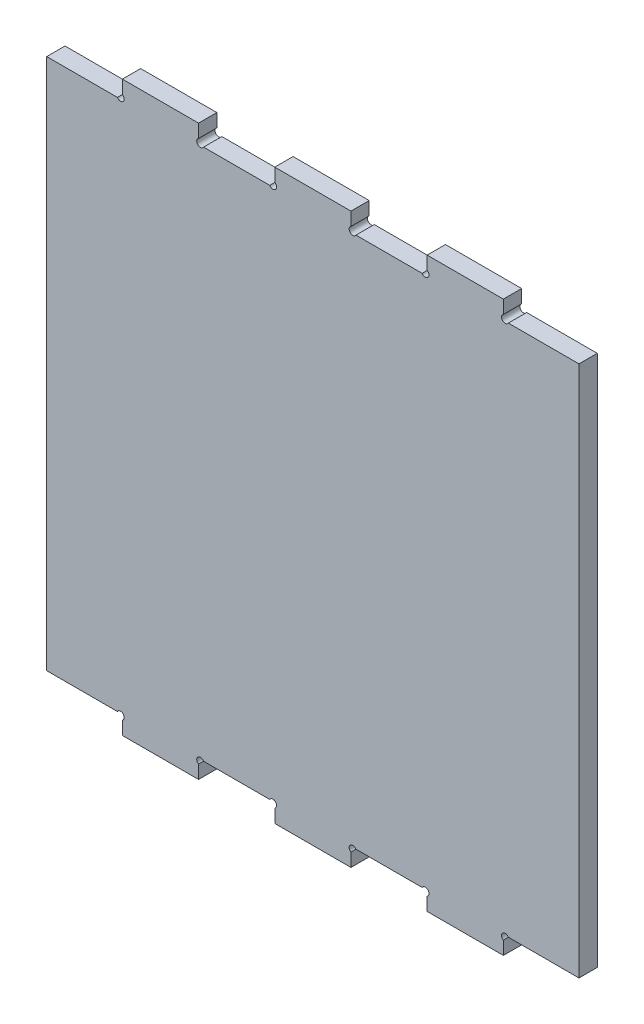
SolidWorks part; units mm, degrees
ref_plane "Front Plane" through (0, 0, 0) normal (0, 0, 1) x (1, 0, 0)
ref_plane "Top Plane" through (0, 0, 0) normal (0, 1, 0) x (1, 0, 0)
ref_plane "Right Plane" through (0, 0, 0) normal (1, 0, 0) x (0, 0, -1)
sketch "Sketch1" plane through (0, 0, 0) normal (0, 0, 1) x (1, 0, 0)
  line L0 (-147.5564, 174.6264) -> (-101.1926, 174.6264)
  line L1 (-97.9177, 186.6264) -> (-47.9177, 186.6264)
  line L2 (-147.5564, 174.6264) -> (-147.5564, -174.3736)
  line L3 (127.0823, -168.3736) -> (127.0823, -214.3646) construction
  line L4 (201.721, 174.6264) -> (201.721, -174.3736)
  line L5 (-97.9177, 168.6264) -> (-47.9177, 168.6264) construction
  line L6 (-47.9177, 186.6264) -> (-47.9177, 177.911)
  line L7 (-44.6428, 174.6264) -> (-1.1926, 174.6264)
  line L8 (2.0823, 177.911) -> (2.0823, 186.6264)
  line L9 (2.0823, 186.6264) -> (52.0823, 186.6264)
  line L10 (52.0823, 186.6264) -> (52.0823, 177.911)
  line L11 (55.3572, 174.6264) -> (98.8074, 174.6264)
  line L12 (102.0823, 177.911) -> (102.0823, 186.6264)
  line L13 (102.0823, 186.6264) -> (152.0823, 186.6264)
  line L14 (152.0823, 186.6264) -> (152.0823, 177.911)
  line L15 (155.3572, 174.6264) -> (201.721, 174.6264)
  line L16 (-72.9177, 168.6264) -> (-72.9177, 194.1917) construction
  line L17 (-47.9177, 168.6264) -> (2.0823, 168.6264) construction
  line L18 (-22.9177, 168.6264) -> (-22.9177, 209.9977) construction
  line L19 (52.0823, 168.6264) -> (102.0823, 168.6264) construction
  line L20 (77.0823, 168.6264) -> (77.0823, 215.5699) construction
  line L21 (2.0823, 168.6264) -> (52.0823, 168.6264) construction
  line L22 (-97.9177, 177.911) -> (-97.9177, 186.6264)
  line L23 (27.0823, 168.6264) -> (27.0823, 205.384) construction
  line L24 (102.0823, 168.6264) -> (152.0823, 168.6264) construction
  line L25 (127.0823, 168.6264) -> (127.0823, 214.6175) construction
  line L26 (139.0222, 186.6264) -> (139.0222, -186.3736) construction
  line L27 (201.721, 0.1264) -> (-147.5564, 0.1264) construction
  line L28 (102.0823, -168.3736) -> (152.0823, -168.3736) construction
  line L29 (27.0823, -168.3736) -> (27.0823, -205.1311) construction
  line L30 (2.0823, -168.3736) -> (52.0823, -168.3736) construction
  line L31 (77.0823, -168.3736) -> (77.0823, -215.317) construction
  line L32 (52.0823, -168.3736) -> (102.0823, -168.3736) construction
  line L33 (-22.9177, -168.3736) -> (-22.9177, -209.7448) construction
  line L34 (-47.9177, -168.3736) -> (2.0823, -168.3736) construction
  line L35 (-72.9177, -168.3736) -> (-72.9177, -193.9388) construction
  line L36 (-97.9177, -168.3736) -> (-47.9177, -168.3736) construction
  line L37 (-97.9177, -177.6582) -> (-97.9177, -186.3736)
  line L38 (155.3572, -174.3736) -> (201.721, -174.3736)
  line L39 (152.0823, -186.3736) -> (152.0823, -177.6582)
  line L40 (102.0823, -186.3736) -> (152.0823, -186.3736)
  line L41 (102.0823, -177.6582) -> (102.0823, -186.3736)
  line L42 (55.3572, -174.3736) -> (98.8074, -174.3736)
  line L43 (52.0823, -186.3736) -> (52.0823, -177.6582)
  line L44 (2.0823, -186.3736) -> (52.0823, -186.3736)
  line L45 (2.0823, -177.6582) -> (2.0823, -186.3736)
  line L46 (-44.6428, -174.3736) -> (-1.1926, -174.3736)
  line L47 (-47.9177, -186.3736) -> (-47.9177, -177.6582)
  line L48 (-97.9177, -186.3736) -> (-47.9177, -186.3736)
  line L49 (-147.5564, -174.3736) -> (-101.1926, -174.3736)
  circle A0 centre (-97.9177, 168.6264) radius 2.4 construction
  arc A1 (-101.1926, 174.6264) -> (-97.9177, 177.911) centre (-99.1177, 175.8326) ccw
  arc A2 (-44.6428, 174.6264) -> (-47.9177, 177.911) centre (-46.7177, 175.8326) cw
  arc A3 (-1.1926, 174.6264) -> (2.0823, 177.911) centre (0.8823, 175.8326) ccw
  arc A4 (55.3572, 174.6264) -> (52.0823, 177.911) centre (53.2823, 175.8326) cw
  arc A5 (98.8074, 174.6264) -> (102.0823, 177.911) centre (100.8823, 175.8326) ccw
  arc A6 (155.3572, 174.6264) -> (152.0823, 177.911) centre (153.2823, 175.8326) cw
  circle A7 centre (-97.9177, -168.3736) radius 2.4 construction
  arc A8 (155.3572, -174.3736) -> (152.0823, -177.6582) centre (153.2823, -175.5797) ccw
  arc A9 (98.8074, -174.3736) -> (102.0823, -177.6582) centre (100.8823, -175.5797) cw
  arc A10 (55.3572, -174.3736) -> (52.0823, -177.6582) centre (53.2823, -175.5797) ccw
  arc A11 (-1.1926, -174.3736) -> (2.0823, -177.6582) centre (0.8823, -175.5797) cw
  arc A12 (-44.6428, -174.3736) -> (-47.9177, -177.6582) centre (-46.7177, -175.5797) ccw
  arc A13 (-101.1926, -174.3736) -> (-97.9177, -177.6582) centre (-99.1177, -175.5797) cw
  dimension "D10" = 4.8
  dimension "D11" = 4.8
  dimension "D1" = 50
  dimension "D2" = 50
  dimension "D3" = 12
  dimension "D4" = 50
  dimension "D5" = 50
  dimension "D6" = 50
  dimension "D7" = 50
  dimension "D8" = 50
  dimension "D9" = 18
extrude "Boss-Extrude1" add sketch "Sketch1" along normal blind 12
